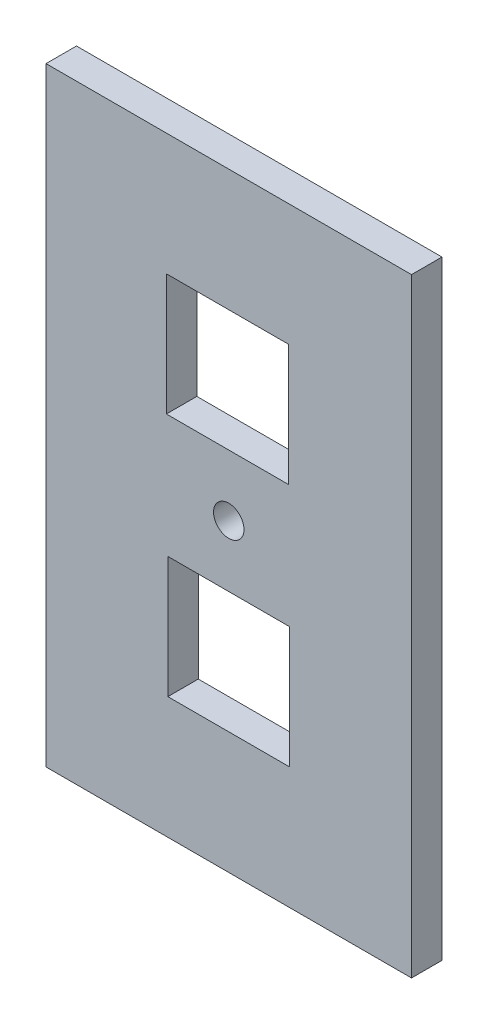
SolidWorks part; units mm, degrees
ref_plane "Front" through (0, 0, 0) normal (0, 0, 1) x (1, 0, 0)
ref_plane "Top" through (0, 0, 0) normal (0, 1, 0) x (1, 0, 0)
ref_plane "Right" through (0, 0, 0) normal (1, 0, 0) x (0, 0, -1)
sketch "Sketch1" plane through (0, 0, 0) normal (0, 0, 1) x (1, 0, 0)
  line L1 (0, 0) -> (76.2, 0)
  line L2 (0, 0) -> (0, 127)
  line L3 (0, 127) -> (76.2, 127)
  line L4 (76.2, 0) -> (76.2, 127)
  line L13 (50.8, 101.6) -> (25.4, 101.6)
  dimension "D1" = 127
  dimension "D5" = 76.2
  dimension "D8" = 25.4
extrude "Boss-Extrude1" add sketch "Sketch1" along normal blind 6.35 contours L2 L3 L4 L1
sketch "Sketch3" plane through (0, 0, 6.35) normal (0, 0, 1) x (1, 0, 0)
  line L0 (38.1, 127) -> (38.1, 0) construction
  line L1 (0, 127) -> (76.2, 127) construction
  line L2 (0, 0) -> (76.2, 0) construction
  line L3 (25.0929, 101.6) -> (50.5868, 101.6)
  line L4 (25.4, 50.7205) -> (50.8, 50.7205)
  line L5 (25.4, 50.7205) -> (25.4, 25.4)
  line L6 (25.4, 25.4) -> (50.8, 25.4)
  line L7 (50.8, 50.7205) -> (50.8, 25.4)
  line L8 (25.4, 50.7205) -> (50.8, 25.4) construction
  line L9 (25.4, 25.4) -> (50.8, 50.7205) construction
  line L10 (25.0929, 101.6) -> (25.0929, 76.2795)
  line L11 (25.0929, 76.2795) -> (50.5868, 76.2795)
  line L12 (50.5868, 101.6) -> (50.5868, 76.2795)
  line L13 (25.0929, 101.6) -> (50.5868, 76.2795) construction
  line L14 (25.0929, 76.2795) -> (50.5868, 101.6) construction
  line L15 (76.2, 0) -> (76.2, 127) construction
  circle A0 centre (38.1, 63.5) radius 3.175
  point P6 (38.1, 38.0603)
  point P11 (37.8399, 88.9397)
  dimension "D4" = 6.35
  dimension "D1" = 25.4
  dimension "D2" = 25.4
  dimension "D3" = 25.4
  dimension "D5" = 25.4
extrude "Cut-Extrude2" cut sketch "Sketch3" against normal blind 6.35
